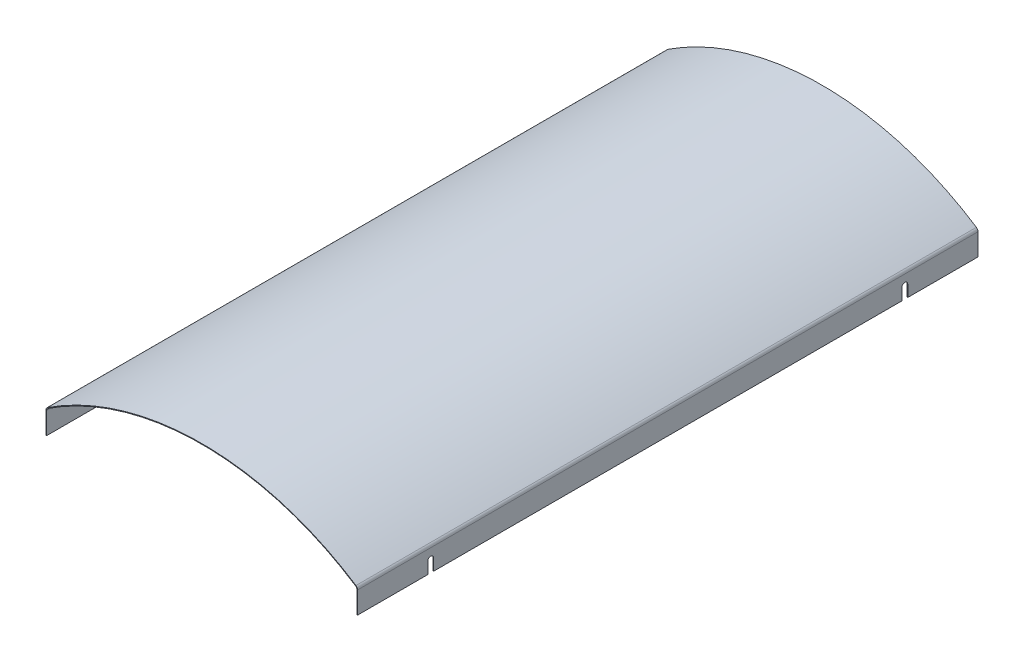
SolidWorks part; units mm, degrees
ref_plane "Front Plane" through (0, 0, 0) normal (0, 0, 1) x (1, 0, 0)
ref_plane "Top Plane" through (0, 0, 0) normal (0, 1, 0) x (1, 0, 0)
ref_plane "Right Plane" through (0, 0, 0) normal (1, 0, 0) x (0, 0, -1)
sketch "Sketch1" plane through (0, 0, 0) normal (0, 0, 1) x (1, 0, 0)
  line L0 (0, 0) -> (0, 1335.722) construction
  line L3 (-336.55, 1067.0777) -> (-336.55, 1114.455)
  line L4 (-330.2, -50.8) -> (-330.2, 1117.6) construction
  line L5 (-330.2, 1117.6) -> (-279.4, 1117.6) construction
  circle A0 centre (0, 609.6) radius 609.6 construction
  arc A1 (-333.6758, 1119.7692) -> (0, 1219.2) centre (0, 609.6) cw
  arc A2 (-336.55, 1114.455) -> (-333.6758, 1119.7692) centre (-330.2, 1114.455) cw
  point P14 (-336.55, 1117.8777)
  dimension "D1" = 1219.2
  dimension "D3" = 6.35
  dimension "D2" = 508
  dimension "D4" = 6.35
  dimension "D5" = 50.8
extrude "Extrude-Thin1" add sketch "Sketch1" along normal mid plane 1346.2 thin thin type one direction reverse wall 1.5
mirror "Mirror1" about plane through (0, 0, 0) normal (1, 0, 0) of "Extrude-Thin1"
sketch "Sketch3" plane through (-338.05, 0, 0) normal (-1, 0, 0) x (0, 0, 1)
  line L0 (508, 1092.2) -> (508, 1067.0777)
  line L1 (673.1, 1067.0777) -> (-673.1, 1067.0777) construction
  line L2 (520.7, 1092.2) -> (520.7, 1067.0777)
  line L3 (520.7, 1067.0777) -> (508, 1067.0777)
  line L4 (0, 1067.0777) -> (0, 1080.1472) construction
  line L5 (-520.7, 1067.0777) -> (-508, 1067.0777)
  line L6 (-520.7, 1092.2) -> (-520.7, 1067.0777)
  line L7 (-508, 1092.2) -> (-508, 1067.0777)
  arc A0 (520.7, 1092.2) -> (508, 1092.2) centre (514.35, 1092.2) ccw construction
  arc A1 (-520.7, 1092.2) -> (-508, 1092.2) centre (-514.35, 1092.2) cw construction
  arc A2 (520.7, 1092.2) -> (508, 1092.2) centre (514.35, 1092.2) ccw
  arc A3 (-520.7, 1092.2) -> (-508, 1092.2) centre (-514.35, 1092.2) cw
  dimension "D1" = 6.35
extrude "Cut-Extrude2" cut sketch "Sketch3" against normal through all
